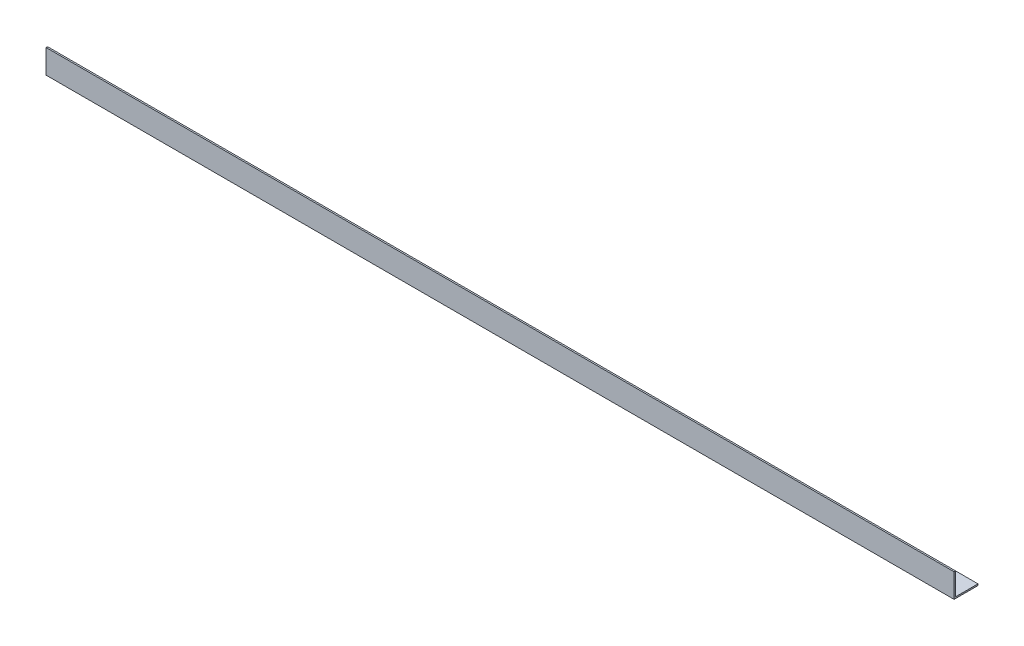
SolidWorks part; units mm, degrees
ref_plane "Alzado" through (0, 0, 0) normal (0, 0, 1) x (1, 0, 0)
ref_plane "Planta" through (0, 0, 0) normal (0, 1, 0) x (1, 0, 0)
ref_plane "Vista lateral" through (0, 0, 0) normal (1, 0, 0) x (0, 0, -1)
sketch "Croquis1" plane through (0, 0, 0) normal (1, 0, 0) x (0, 0, -1)
  line L0 (0, 16) -> (0, 0)
  line L1 (0, 0) -> (16, 0)
  line L2 (16, 0) -> (16, 1)
  line L3 (16, 1) -> (1, 1)
  line L4 (1, 1) -> (1, 16)
  line L5 (1, 16) -> (0, 16)
  dimension "D1" = 16
  dimension "D2" = 16
  dimension "D3" = 1
extrude "Saliente-Extruir1" add sketch "Croquis1" along normal blind 607
